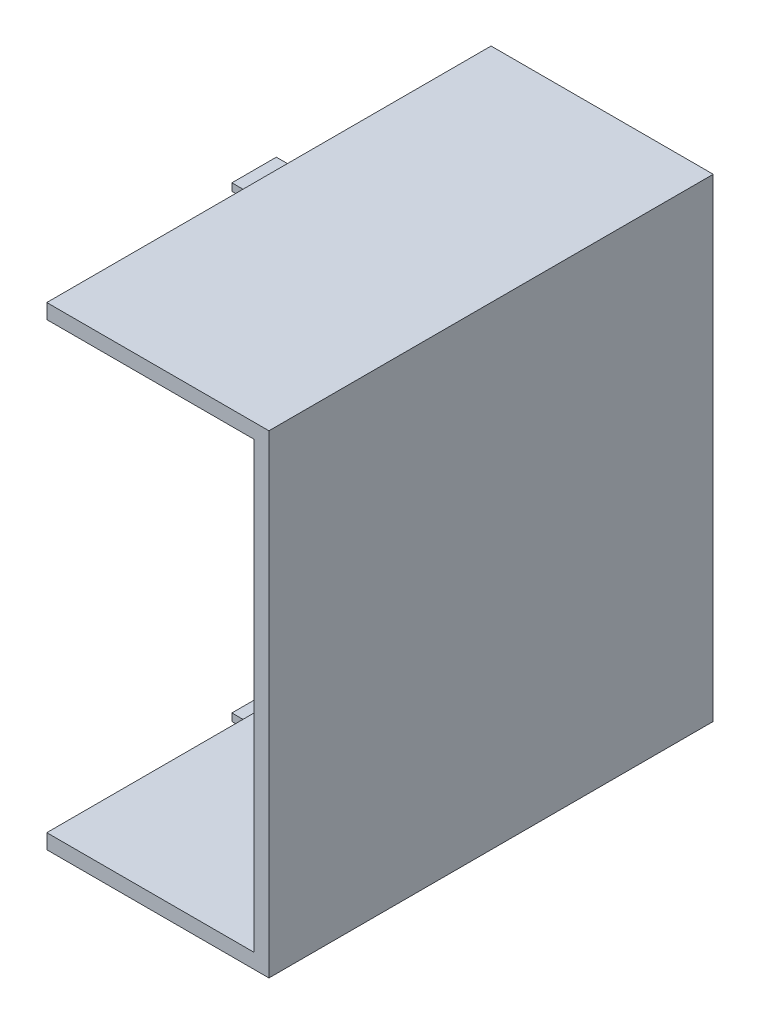
SolidWorks part; units mm, degrees
ref_plane "Front Plane" through (0, 0, 0) normal (0, 0, 1) x (1, 0, 0)
ref_plane "Top Plane" through (0, 0, 0) normal (0, 1, 0) x (1, 0, 0)
ref_plane "Right Plane" through (0, 0, 0) normal (1, 0, 0) x (0, 0, -1)
sketch "Sketch1" plane through (0, 0, 0) normal (0, 0, 1) x (1, 0, 0)
  line L0 (0, 0) -> (15, 0)
  line L1 (15, 0) -> (15, 32)
  line L2 (15, 32) -> (0, 32)
  line L3 (0, 32) -> (0, 31)
  line L4 (0, 31) -> (14, 31)
  line L5 (14, 31) -> (14, 1)
  line L6 (14, 1) -> (0, 1)
  line L7 (0, 1) -> (0, 0)
  dimension "D1" = 15
  dimension "D2" = 1
  dimension "D3" = 32
  dimension "D4" = 1
  dimension "D5" = 1
extrude "Boss-Extrude1" add sketch "Sketch1" along normal mid plane 30 contours L5 L6 L7 L0 L1 L2 L3 L4
sketch "Sketch2" plane through (0, 0, 0) normal (-1, 0, 0) x (0, 0, 1)
  line L0 (15, 32) -> (15, 31) construction
  line L1 (-1.5, 31.75) -> (1.5, 31.75)
  line L2 (-1.5, 31.75) -> (-1.5, 31.25)
  line L3 (-1.5, 31.25) -> (1.5, 31.25)
  line L4 (1.5, 31.75) -> (1.5, 31.25)
  line L5 (15, 31) -> (-15, 31) construction
  dimension "D1" = 3
  dimension "D2" = 13.5
  dimension "D3" = 0.25
  dimension "D4" = 0.5
sketch "Sketch3" plane through (0, 0, 0) normal (-1, 0, 0) x (0, 0, 1)
  line L0 (15, 1) -> (15, 0) construction
  line L1 (-1.5, 0.75) -> (1.5, 0.75)
  line L2 (-1.5, 0.75) -> (-1.5, 0.25)
  line L3 (-1.5, 0.25) -> (1.5, 0.25)
  line L4 (1.5, 0.75) -> (1.5, 0.25)
  line L5 (15, 0) -> (-15, 0) construction
  dimension "D1" = 3
  dimension "D2" = 13.5
  dimension "D3" = 0.25
  dimension "D4" = 0.5
extrude "Boss-Extrude2" add sketch "Sketch2" along normal blind 1
extrude "Boss-Extrude3" add sketch "Sketch3" along normal blind 1
